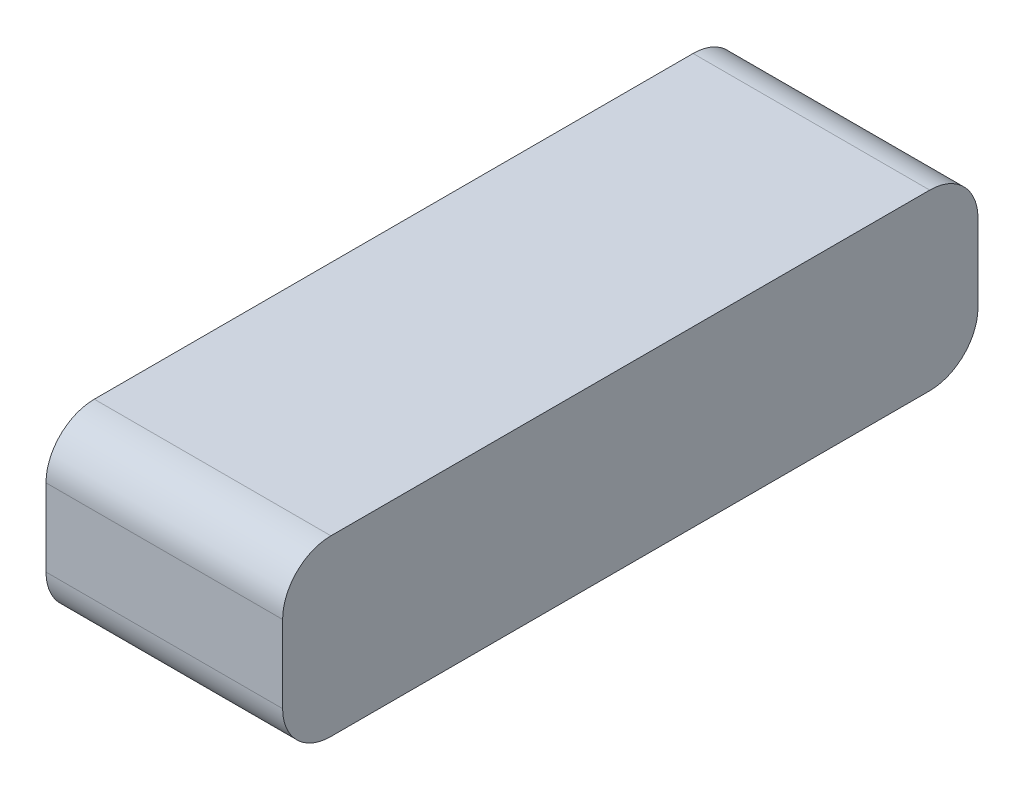
SolidWorks part; units mm, degrees
ref_plane "Piano frontale" through (0, 0, 0) normal (0, 0, 1) x (1, 0, 0)
ref_plane "Piano superiore" through (0, 0, 0) normal (0, 1, 0) x (1, 0, 0)
ref_plane "Piano destro" through (0, 0, 0) normal (1, 0, 0) x (0, 0, -1)
sketch "Schizzo1" plane through (0, 0, 0) normal (0, 0, 1) x (1, 0, 0)
  line L1 (-24.5, -18) -> (24.5, -18)
  line L2 (-24.5, -18) -> (-24.5, 18)
  line L3 (-24.5, 18) -> (24.5, 18)
  line L4 (24.5, -18) -> (24.5, 18)
  line L5 (-24.5, -18) -> (24.5, 18) construction
  line L6 (-24.5, 18) -> (24.5, -18) construction
  point P0 (0, 0)
  dimension "D1" = 49
  dimension "D2" = 36
extrude "Estrusione-Estrusione1" add sketch "Schizzo1" along normal blind 144
fillet "Raccordo1" radius 10 4 edges at (0, 18, 0) (0, -18, 0) (0, -18, 144) (0, 18, 144)
